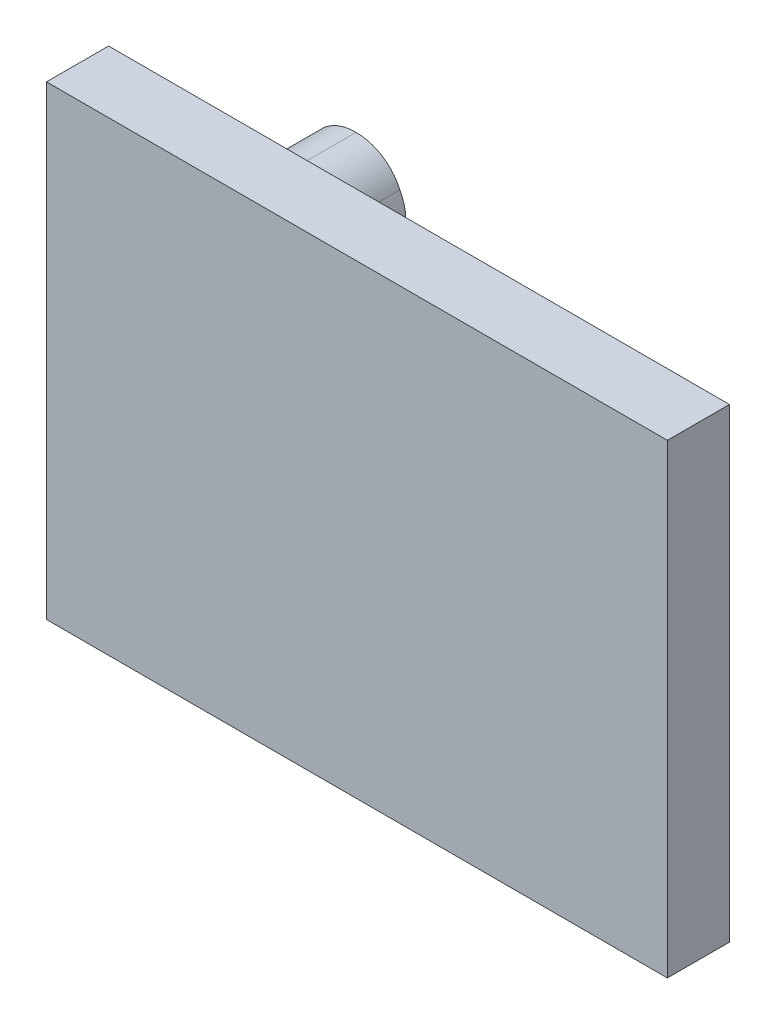
SolidWorks part; units mm, degrees
ref_plane "Front Plane" through (0, 0, 0) normal (0, 0, 1) x (1, 0, 0)
ref_plane "Top Plane" through (0, 0, 0) normal (0, 1, 0) x (1, 0, 0)
ref_plane "Right Plane" through (0, 0, 0) normal (1, 0, 0) x (0, 0, -1)
sketch "Sketch1" plane through (0, 0, 0) normal (0, 0, 1) x (1, 0, 0)
  line L1 (-100, -75) -> (100, -75)
  line L2 (-100, -75) -> (-100, 75)
  line L3 (-100, 75) -> (100, 75)
  line L4 (100, -75) -> (100, 75)
  line L5 (-100, -75) -> (100, 75) construction
  line L6 (-100, 75) -> (100, -75) construction
  point P0 (0, 0)
  dimension "D1" = 200
  dimension "D2" = 150
extrude "Boss-Extrude1" add sketch "Sketch1" along normal blind 20
sketch "min" plane through (0, 0, 0) normal (0, 0, -1) x (-1, 0, 0)
  line L0 (-100, -75) -> (-100, 75) construction
  line L1 (100, -75) -> (-100, -75) construction
  line L2 (49.4, 44.4) -> (18.6221, 44.4) construction
  line L3 (49.4, 44.4) -> (49.4, 91.1911) construction
  circle A0 centre (-50.3, -45.3) radius 10.15
  circle A1 centre (49.4, 44.4) radius 15.15
  dimension "D1" = 20.3
  dimension "D2" = 30.3
  dimension "D3" = 49.7
  dimension "D4" = 29.7
  dimension "D5" = 89.7
  dimension "D6" = 99.7
extrude "Boss-Extrude3" add sketch "min" along normal blind 30
sketch "max - lentgh" plane through (0, 0, 0) normal (0, 0, -1) x (-1, 0, 0)
  line L0 (-100, -75) -> (-100, 75) construction
  line L1 (100, -75) -> (-100, -75) construction
  line L2 (50, 45.6) -> (21.8833, 45.6) construction
  line L3 (50, 45.6) -> (50, 89.1432) construction
  circle A0 centre (-50, -44.7) radius 10.15
  circle A1 centre (50, 45.6) radius 15.15
  dimension "D1" = 20.3
  dimension "D2" = 30.3
  dimension "D3" = 50
  dimension "D4" = 30.3
  dimension "D5" = 90.3
  dimension "D6" = 100
extrude "Boss-Extrude4" add sketch "max - lentgh" along normal blind 30
sketch "max - width" plane through (0, 0, 0) normal (0, 0, -1) x (-1, 0, 0)
  line L0 (-100, -75) -> (-100, 75) construction
  line L1 (100, -75) -> (-100, -75) construction
  line L2 (50.6, 45) -> (32.6016, 45) construction
  line L3 (50.6, 45) -> (50.6, 74.922) construction
  circle A0 centre (-49.7, -45) radius 10.15
  circle A1 centre (50.6, 45) radius 15.15
  dimension "D1" = 20.3
  dimension "D2" = 30.3
  dimension "D3" = 50.3
  dimension "D4" = 30
  dimension "D5" = 90
  dimension "D6" = 100.3
extrude "Boss-Extrude5" add sketch "max - width" along normal blind 30
sketch "max" plane through (0, 0, 0) normal (0, 0, -1) x (-1, 0, 0)
  line L0 (-100, -75) -> (-100, 75) construction
  line L1 (100, -75) -> (-100, -75) construction
  line L2 (50.6, 45.6) -> (24.3395, 45.6) construction
  line L3 (50.6, 45.6) -> (50.6, 82.8909) construction
  circle A0 centre (-49.7, -44.7) radius 10.15
  circle A1 centre (50.6, 45.6) radius 15.15
  dimension "D1" = 20.3
  dimension "D2" = 30.3
  dimension "D3" = 50.3
  dimension "D4" = 30.3
  dimension "D5" = 90.3
  dimension "D6" = 100.3
extrude "Boss-Extrude6" add sketch "max" along normal blind 30
sketch "Sketch7" plane through (0, 0, 0) normal (0, 0, -1) x (-1, 0, 0)
  line L0 (-100, -75) -> (-100, 75) construction
  line L1 (100, -75) -> (-100, -75) construction
  line L2 (50.6, 45.6) -> (10.6843, 45.6) construction
  line L3 (50.6, 45.6) -> (50.6, 83.6949) construction
  circle A0 centre (-49.7, -44.7) radius 11.25
  circle A1 centre (50.6, 45.6) radius 17
  dimension "D3" = 22.5
  dimension "D6" = 34
  dimension "D1" = 50.3
  dimension "D2" = 30.3
  dimension "D4" = 90.3
  dimension "D5" = 100.3
